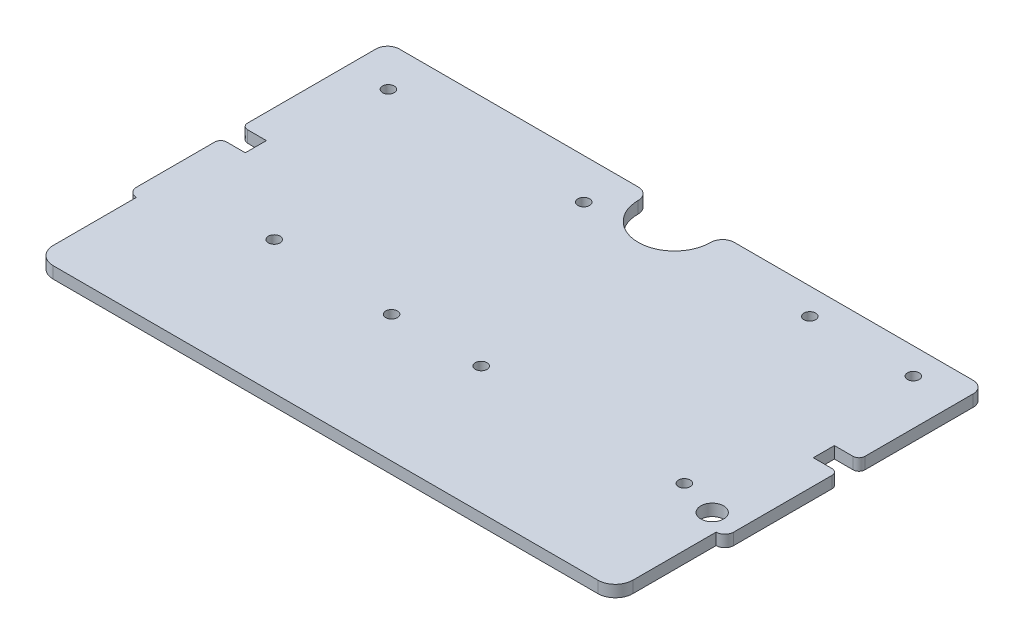
SolidWorks part; units mm, degrees
ref_plane "Front Plane" through (0, 0, 0) normal (0, 0, 1) x (1, 0, 0)
ref_plane "Top Plane" through (0, 0, 0) normal (0, 1, 0) x (1, 0, 0)
ref_plane "Right Plane" through (0, 0, 0) normal (1, 0, 0) x (0, 0, -1)
sketch "Sketch1" plane through (0, 0, 0) normal (0, 1, 0) x (1, 0, 0)
  line L0 (0, -1) -> (0, -21.45)
  line L1 (0.75, -22.2) -> (0.75, -29.3)
  line L2 (2.25, -30.8) -> (48.75, -30.8)
  line L3 (50.25, -29.3) -> (50.25, -22.2)
  line L4 (51, -21.45) -> (51, -1)
  line L5 (50, 0) -> (1, 0)
  line L7 (1, 0) -> (0, 0) construction
  line L8 (0, 0) -> (0, -1) construction
  arc A0 (0, -21.45) -> (0.75, -22.2) centre (0.75, -21.45) ccw
  arc A3 (50.25, -22.2) -> (51, -21.45) centre (50.25, -21.45) ccw
  arc A4 (51, -1) -> (50, 0) centre (50, -1) ccw
  arc A5 (1, 0) -> (0, -1) centre (1, -1) ccw
  arc A6 (48.75, -30.8) -> (50.25, -29.3) centre (48.75, -29.3) ccw
  arc A7 (0.75, -29.3) -> (2.25, -30.8) centre (2.25, -29.3) ccw
  point P0 (3.5262, -3.5262)
  point P19 (0.75, -30.8)
  dimension "D5" = 1.5
  dimension "D6" = 1
  dimension "D1" = 0.75
  dimension "D2" = 51
  dimension "D3" = 0.75
  dimension "D4" = 8.6
  dimension "D7" = 30.8
extrude "Boss-Extrude1" add sketch "Sketch1" along normal blind 1
sketch "Sketch2" plane through (0, 1, 0) normal (0, 1, 0) x (1, 0, 0)
  line L0 (21.4, 0) -> (29.6, 0)
  line L1 (50, 0) -> (1, 0) construction
  line L2 (0, -12.45) -> (2.1, -12.45)
  line L3 (0, -1) -> (0, -21.45) construction
  line L4 (2.1, -12.45) -> (2.1, -14.25)
  line L5 (2.1, -14.25) -> (0, -14.25)
  line L6 (0, -14.25) -> (0, -12.45)
  line L7 (51, -10.75) -> (48.9, -10.75)
  line L8 (51, -21.45) -> (51, -1) construction
  line L9 (48.9, -10.75) -> (48.9, -12.55)
  line L10 (48.9, -12.55) -> (51, -12.55)
  line L11 (51, -12.55) -> (51, -10.75)
  arc A0 (29.6, 0) -> (28.6, -1) centre (29.6, -1) ccw
  arc A1 (28.6, -1) -> (22.4, -1) centre (25.5, -1) cw
  arc A2 (22.4, -1) -> (21.4, 0) centre (21.4, -1) ccw
  point P19 (30.1903, 0)
  point P22 (19.5171, 0)
  point P23 (18.8459, 0)
  point P24 (0, 0)
  point P25 (20.3602, -1.2518)
  point P26 (25.5, -0.9999)
  point P27 (25.5, -0.9611)
  point P28 (0, 0)
  line M20 (51, -21.45) -> (51, -1)
  line M22 (50, 0) -> (1, 0)
  line M24 (0, -1) -> (0, -21.45)
  dimension "D2" = 1
  dimension "D1" = 6.2
  dimension "D3" = 25.5
  dimension "D4" = 12.45
  dimension "D5" = 10.75
  dimension "D6" = 1.8
  dimension "D7" = 1.8
  dimension "D8" = 2.1
  dimension "D9" = 2.1
extrude "Cut-Extrude1" cut sketch "Sketch2" against normal through all both and the other way through all contours L5 L4 L2 M24 | A2 A1 A0 M22 | L9 L10 L7 M20
fillet "Fillet1" radius 0.5 4 edges at (0, 0.5, 14.25) (0, 0.5, 12.45) (51, 0.5, 12.55) (51, 0.5, 10.75)
sketch "Sketch3" plane through (0, 1, 0) normal (0, 1, 0) x (1, 0, 0)
  line L0 (0.75, -22.2) -> (0.75, -29.3) construction
  line L1 (2.25, -30.8) -> (48.75, -30.8) construction
  line L2 (51, -21.45) -> (51, -13.05) construction
  line L3 (0, -1) -> (0, -11.95) construction
  line L4 (21.4, 0) -> (1, 0) construction
  line L5 (51, -10.25) -> (51, -1) construction
  line L6 (50, 0) -> (29.6, 0) construction
  circle A0 centre (3.52, -3.45) radius 0.5
  circle A1 centre (20.2, -3.45) radius 0.5
  circle A2 centre (38.3, -2.25) radius 0.5
  circle A3 centre (47.14, -2.25) radius 0.5
  circle A4 centre (45.29, -19.95) radius 0.5
  circle A5 centre (27.94, -19.95) radius 0.5
  circle A6 centre (20.29, -19.95) radius 0.5
  circle A7 centre (9.75, -19.43) radius 0.5
  circle A8 centre (48.627, -20.91) radius 0.975
  point P24 (0, 0)
  point P29 (0, 0)
  point P34 (0, 0)
  point P35 (0, 0)
  dimension "D1" = 1
  dimension "D9" = 1.95
  dimension "D2" = 9
  dimension "D3" = 10.54
  dimension "D4" = 7.65
  dimension "D5" = 17.35
  dimension "D6" = 9.89
  dimension "D7" = 2.373
  dimension "D8" = 10.85
  dimension "D10" = 11.37
  dimension "D11" = 3.52
  dimension "D12" = 3.86
  dimension "D13" = 20.2
  dimension "D14" = 3.45
  dimension "D15" = 12.7
  dimension "D16" = 2.25
extrude "Cut-Extrude2" cut sketch "Sketch3" against normal through all both contours A0 | A1 | A2 | A3 | A8 | A4 | A5 | A6 | A7
